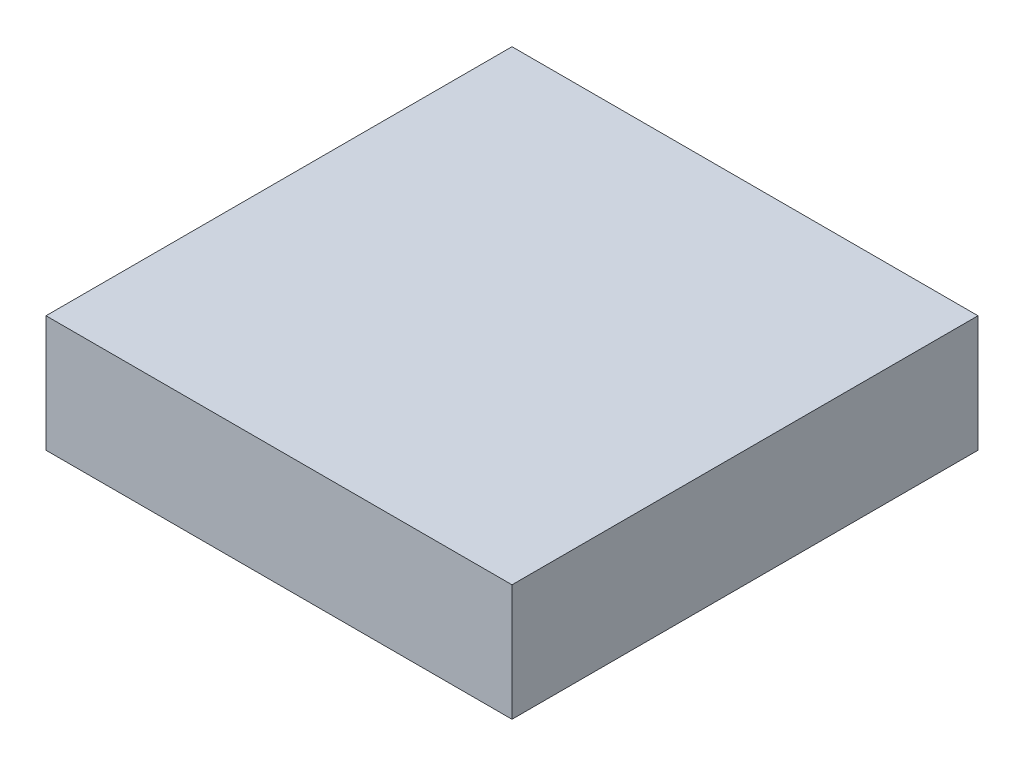
SolidWorks part; units mm, degrees
ref_plane "Front Plane" through (0, 0, 0) normal (0, 0, 1) x (1, 0, 0)
ref_plane "Top Plane" through (0, 0, 0) normal (0, 1, 0) x (1, 0, 0)
ref_plane "Right Plane" through (0, 0, 0) normal (1, 0, 0) x (0, 0, -1)
sketch "Sketch1" plane through (0, 0, 0) normal (0, 1, 0) x (1, 0, 0)
  line L1 (10, 10) -> (-10, 10)
  line L2 (10, 10) -> (10, -10)
  line L3 (10, -10) -> (-10, -10)
  line L4 (-10, 10) -> (-10, -10)
  line L5 (10, 10) -> (-10, -10) construction
  line L6 (10, -10) -> (-10, 10) construction
  point P0 (0, 0)
  dimension "D1" = 20
  dimension "D2" = 20
extrude "Boss-Extrude1" add sketch "Sketch1" along normal blind 5
equation "\"D2@Sketch1\"=\"D1@Sketch1\""
